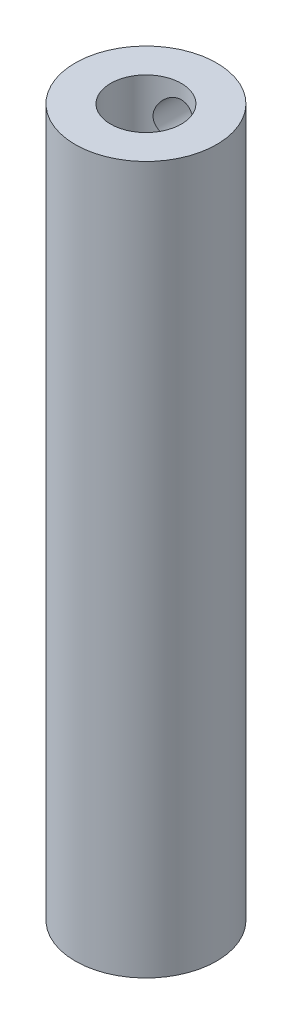
SolidWorks part; units mm, degrees
ref_plane "Front Plane" through (0, 0, 0) normal (0, 0, 1) x (1, 0, 0)
ref_plane "Top Plane" through (0, 0, 0) normal (0, 1, 0) x (1, 0, 0)
ref_plane "Right Plane" through (0, 0, 0) normal (1, 0, 0) x (0, 0, -1)
sketch "Sketch1" plane through (0, 0, 0) normal (0, 1, 0) x (1, 0, 0)
  circle A0 centre (0, 0) radius 10
  dimension "D1" = 20
extrude "Boss-Extrude1" add sketch "Sketch1" along normal blind 100
sketch "Sketch2" plane through (0, 100, 0) normal (0, 1, 0) x (1, 0, 0)
  circle A0 centre (0, 0) radius 5
extrude "Cut-Extrude1" cut sketch "Sketch2" against normal blind 20
sketch "Sketch3" plane through (0, 0, 0) normal (0, 0, 1) x (1, 0, 0)
  line L0 (5, 100) -> (-5, 100) construction
  line L1 (0, 100) -> (0, 0) construction
  circle A0 centre (0, 95) radius 3
  point P4 (0, 0)
  dimension "D1" = 5
extrude "Cut-Extrude2" cut sketch "Sketch3" against normal blind 18
